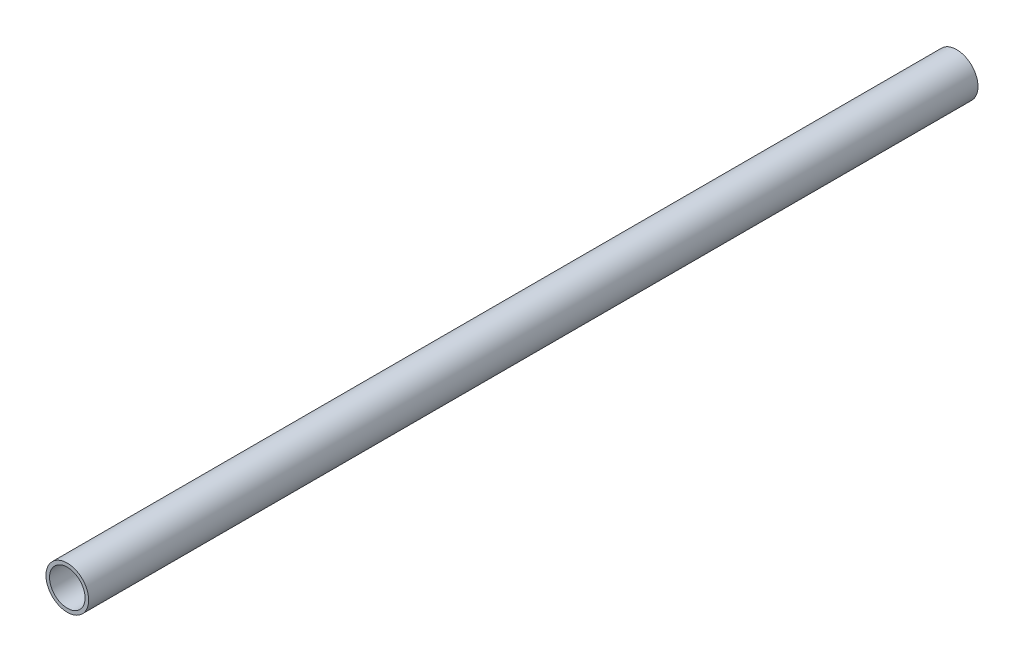
SolidWorks part; units mm, degrees
ref_plane "前视基准面" through (0, 0, 0) normal (0, 0, 1) x (1, 0, 0)
ref_plane "上视基准面" through (0, 0, 0) normal (0, 1, 0) x (1, 0, 0)
ref_plane "右视基准面" through (0, 0, 0) normal (1, 0, 0) x (0, 0, -1)
sketch "草图1" plane through (0, 0, 0) normal (0, 0, 1) x (1, 0, 0)
  circle A0 centre (0, 0) radius 6
extrude "凸台-拉伸1" add sketch "草图1" along normal blind 250
sketch "草图2" plane through (0, 0, 0) normal (0, 0, -1) x (-1, 0, 0)
  circle A0 centre (0, 0) radius 5
extrude "切除-拉伸1" cut sketch "草图2" against normal blind 300 contours A0
